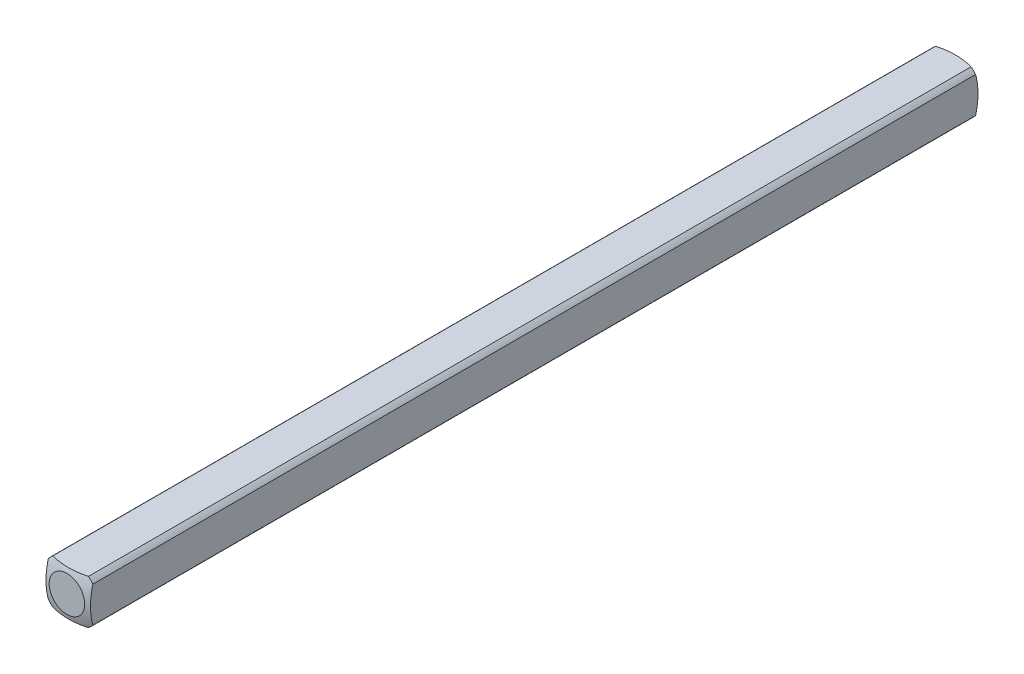
SolidWorks part; units mm, degrees
material "Custom Plastic"
ref_plane "Front Plane" through (0, 0, 0) normal (0, 0, 1) x (1, 0, 0)
ref_plane "Top Plane" through (0, 0, 0) normal (0, 1, 0) x (1, 0, 0)
ref_plane "Right Plane" through (0, 0, 0) normal (1, 0, 0) x (0, 0, -1)
sketch "Sketch1" plane through (0, 0, 0) normal (0, 0, 1) x (1, 0, 0)
  line L0 (-1.5875, -1.5875) -> (1.5875, 1.5875) construction
  line L1 (-1.5875, -1.5875) -> (1.5875, -1.5875)
  line L2 (-1.5875, -1.5875) -> (-1.5875, 1.5875)
  line L3 (-1.5875, 1.5875) -> (1.5875, 1.5875)
  line L4 (1.5875, -1.5875) -> (1.5875, 1.5875)
  dimension "D1" = 3.175
extrude "Boss-Extrude1" add sketch "Sketch1" along normal blind 31.75
sketch "Sketch2" plane through (0, 0, 0) normal (0, 0, -1) x (-1, 0, 0)
  circle A0 centre (0, 0) radius 2.032
  dimension "D1" = 4.064
extrude "Cut-Extrude1" cut sketch "Sketch2" against normal through all flip side to cut
ref_axis "Axis1" through (0, 0, 31.75) along (0, 0, -1)
sketch "Sketch3" plane through (0, 0, 0) normal (0, 1, 0) x (1, 0, 0)
  line L1 (-5.0537, -4.4027) -> (-5.0537, 5.7405)
  line L2 (-5.0537, 5.7405) -> (0, 5.7405)
  line L5 (0, -31.75) -> (0, 0) construction
  line L8 (0, 0.1609) -> (0, 5.7405)
  arc A0 (-5.0537, -4.4027) -> (0, 0.1609) centre (0, -4.9191) cw
  dimension "D1" = 5.08
revolve "Cut-Revolve1" cut sketch "Sketch3" angle 360 about axis through (0, 0, 31.75) along (0, 0, -1)
mirror "Mirror1" about plane through (0, 0, 31.75) normal (0, 0, -1) of bodies 103
